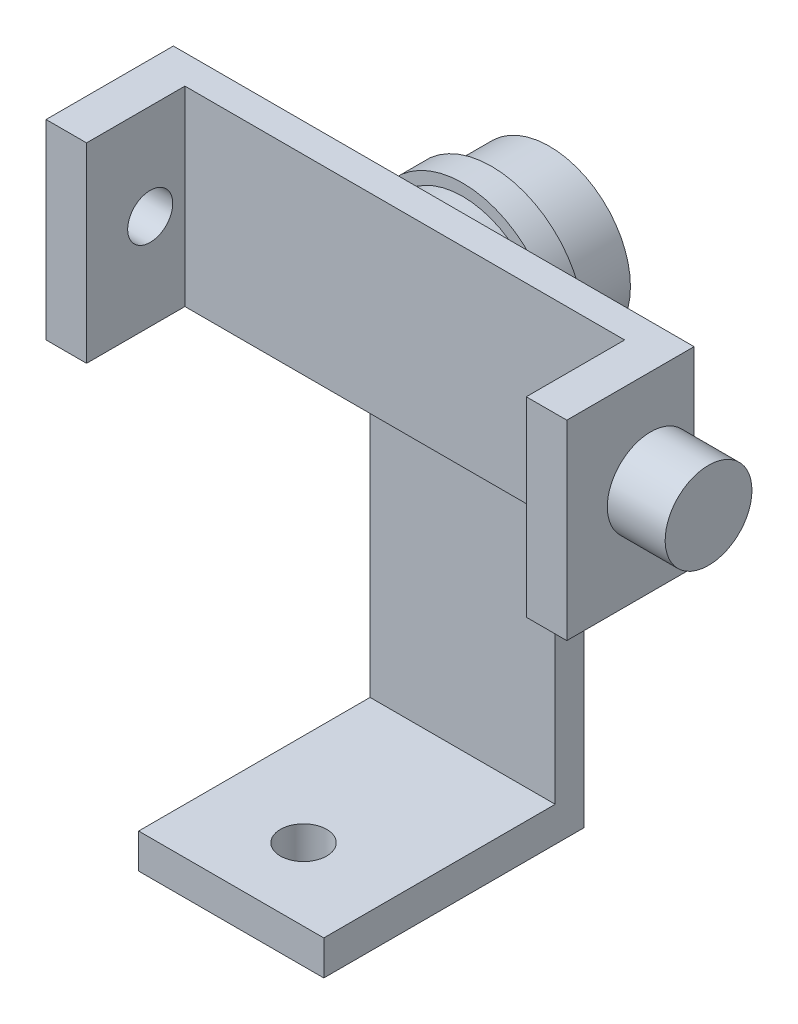
SolidWorks part; units mm, degrees
ref_plane "Front Plane" through (0, 0, 0) normal (0, 0, 1) x (1, 0, 0)
ref_plane "Top Plane" through (0, 0, 0) normal (0, 1, 0) x (1, 0, 0)
ref_plane "Right Plane" through (0, 0, 0) normal (1, 0, 0) x (0, 0, -1)
sketch "Sketch1" plane through (0, 0, 0) normal (0, 1, 0) x (1, 0, 0)
  line L1 (-16, 32.5) -> (16, 32.5)
  line L2 (-16, 32.5) -> (-16, -12.5)
  line L3 (-16, -12.5) -> (16, -12.5)
  line L4 (16, 32.5) -> (16, -12.5)
  circle A0 centre (0, 0) radius 4
  dimension "D1" = 8
  dimension "D2" = 32
  dimension "D3" = 45
  dimension "D4" = 12.5
  dimension "D5" = 16
extrude "Boss-Extrude1" add sketch "Sketch1" along normal blind 6
sketch "Sketch2" plane through (0, 6, 0) normal (0, 1, 0) x (1, 0, 0)
  line L0 (16, -12.5) -> (16, 32.5) construction
  line L1 (-16, 32.5) -> (16, 32.5)
  line L2 (-16, 32.5) -> (-16, 27.5)
  line L3 (-16, 27.5) -> (16, 27.5)
  line L4 (16, 32.5) -> (16, 27.5)
  dimension "D1" = 5
extrude "Boss-Extrude2" add sketch "Sketch2" along normal blind 85
sketch "Sketch3" plane through (0, 0, -27.5) normal (0, 0, 1) x (1, 0, 0)
  line L2 (-16, 91) -> (-16, 6) construction
  line L3 (16, 91) -> (16, 6) construction
  line L4 (-16, 75) -> (16, 75)
  arc A0 (-16, 75) -> (16, 75) centre (0, 75) cw
  point P0 (-16, 75)
  line M4 (16, 6) -> (16, 91)
  line M5 (16, 91) -> (-16, 91)
  line M6 (-16, 91) -> (-16, 6)
  dimension "D1" = 16
extrude "Cut-Extrude1" cut sketch "Sketch3" against normal blind 85 contours A0 M6 M5 | A0 M5 M4
sketch "Sketch4" plane through (0, 0, -27.5) normal (0, 0, 1) x (1, 0, 0)
  line L0 (-16, 75) -> (16, 75)
  arc A1 (16, 75) -> (-16, 75) centre (0, 75) ccw construction
  circle A2 centre (0, 75) radius 14
extrude "Boss-Extrude4" add sketch "Sketch4" along normal blind 5 and the other way blind 15 contours L0 A2 | L0 A2
sketch "Sketch5" plane through (0, 0, -22.5) normal (0, 0, 1) x (1, 0, 0)
  line L1 (-45, 91.5) -> (45, 91.5)
  line L2 (-45, 91.5) -> (-45, 58.5)
  line L3 (-45, 58.5) -> (45, 58.5)
  line L4 (45, 91.5) -> (45, 58.5)
  point P4 (0, 75)
  dimension "D1" = 90
  dimension "D2" = 33
  dimension "D3" = 45
  dimension "D4" = 16.5
extrude "Boss-Extrude5" add sketch "Sketch5" along normal blind 5
sketch "Sketch6" plane through (0, 0, -17.5) normal (0, 0, 1) x (1, 0, 0)
  line L0 (-45, 58.5) -> (45, 58.5) construction
  line L1 (-45, 91.5) -> (-38, 91.5)
  line L2 (-45, 91.5) -> (-45, 58.5)
  line L3 (-45, 58.5) -> (-38, 58.5)
  line L4 (-38, 91.5) -> (-38, 58.5)
  line L10 (45, 91.5) -> (38, 91.5)
  line L11 (45, 91.5) -> (45, 58.5)
  line L12 (45, 58.5) -> (38, 58.5)
  line L13 (38, 91.5) -> (38, 58.5)
  dimension "D1" = 7
  dimension "D2" = 7
extrude "Boss-Extrude6" add sketch "Sketch6" along normal blind 17
sketch "Sketch7" plane through (45, 0, 0) normal (1, 0, 0) x (0, 0, -1)
  line L0 (0.5, 91.5) -> (22.5, 91.5) construction
  circle A0 centre (15, 75) radius 7.5
  dimension "D1" = 15
  dimension "D2" = 7.5
  dimension "D3" = 16.5
extrude "Boss-Extrude7" add sketch "Sketch7" along normal blind 10
sketch "Sketch8" plane through (-45, 0, 0) normal (-1, 0, 0) x (0, 0, 1)
  circle A0 centre (-11.5, 75) radius 3.8947
  dimension "D1" = 16.5
  dimension "D2" = 11
extrude "Cut-Extrude2" cut sketch "Sketch8" against normal blind 10
